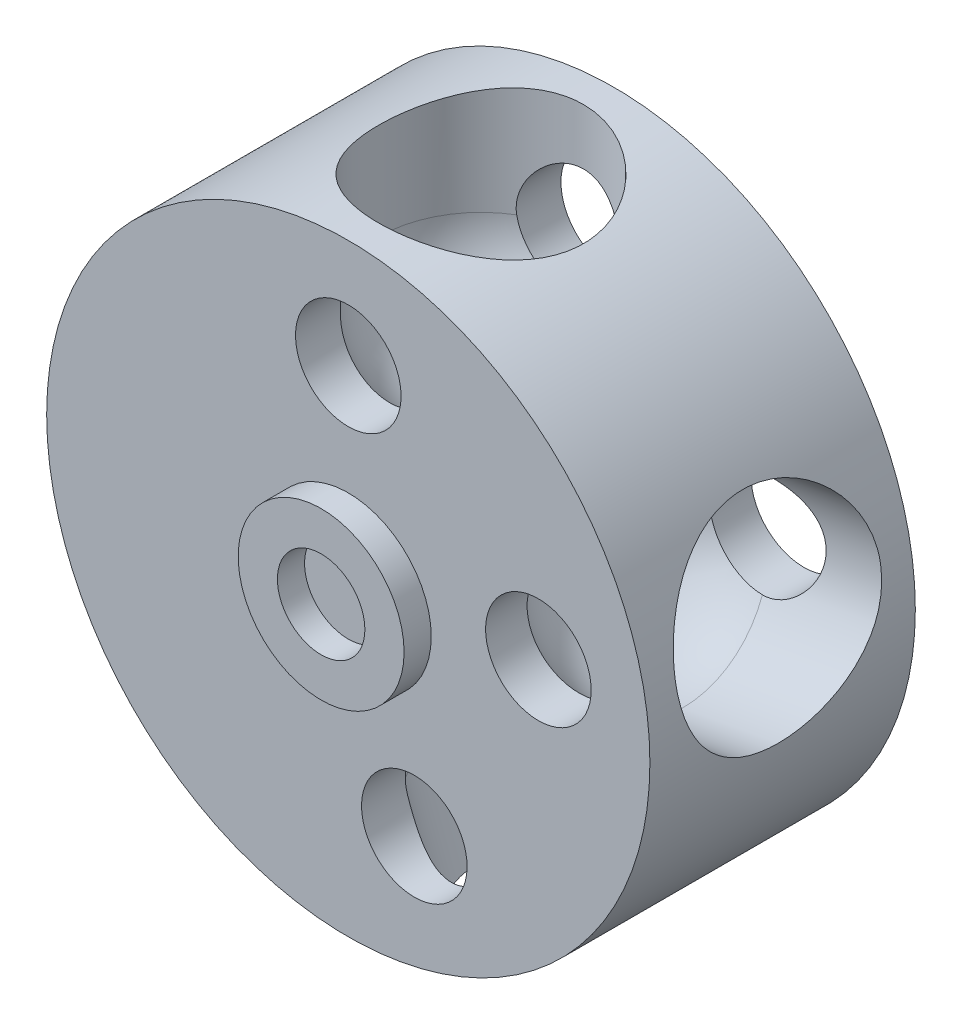
SolidWorks part; units mm, degrees
ref_plane "Front Plane" through (0, 0, 0) normal (0, 0, 1) x (1, 0, 0)
ref_plane "Top Plane" through (0, 0, 0) normal (0, 1, 0) x (1, 0, 0)
ref_plane "Right Plane" through (0, 0, 0) normal (1, 0, 0) x (0, 0, -1)
sketch "Sketch1" plane through (0, 0, 0) normal (0, 0, 1) x (1, 0, 0)
  circle A0 centre (0, 0) radius 25.4
  dimension "D1" = 50.8
extrude "Boss-Extrude1" add sketch "Sketch1" along normal blind 22.352 contours A0
ref_plane "Plane1" through (0, 0, 11.176) normal (0, 0, -1) x (-1, 0, 0)
sketch "Sketch2" plane through (0, 0, 11.176) normal (0, 0, -1) x (-1, 0, 0)
  line L0 (0, 0) -> (0, 25.4) construction
  line L1 (0, 25.4) -> (8.636, 25.4)
  line L2 (8.636, 25.4) -> (8.636, 15.748)
  line L3 (0, 7.112) -> (0, 25.4)
  circle A0 centre (0, 0) radius 25.4 construction
  arc A1 (0, 7.112) -> (8.636, 15.748) centre (0, 15.748) ccw
  dimension "D2" = 17.272
  dimension "D1" = 8.636
  dimension "D3" = 9.652
  dimension "D4" = 9.652
revolve "Cut-Revolve1" cut sketch "Sketch2" angle 360 about L0
sketch "Sketch3" plane through (0, 0, 11.176) normal (0, 0, -1) x (-1, 0, 0)
  line L0 (0, 25.4) -> (0, 7.112) construction
  line L1 (0, 25.4) -> (0, 15.748) construction
  line L2 (0, 20.9296) -> (0, 5.3848) construction
  circle A0 centre (0, 0) radius 25.4 construction
  circle A1 centre (0, 16.256) radius 4.445
  dimension "D2" = 8.89
  dimension "D1" = 18.288
extrude "Cut-Extrude1" cut sketch "Sketch3" against normal through all and the other way through all
pattern_circular "CirPattern1" count 3 over 160 about axis through (0, 0, 0) along (0, 0, 1) of "Cut-Revolve1", "Cut-Extrude1"
sketch "Sketch4" plane through (0, 0, 22.352) normal (0, 0, 1) x (1, 0, 0)
  circle A0 centre (0, 0) radius 6.985
  circle A1 centre (0, 0) radius 3.683
  dimension "D1" = 13.97
  dimension "D2" = 7.366
extrude "Boss-Extrude2" add sketch "Sketch4" along normal blind 2.286
